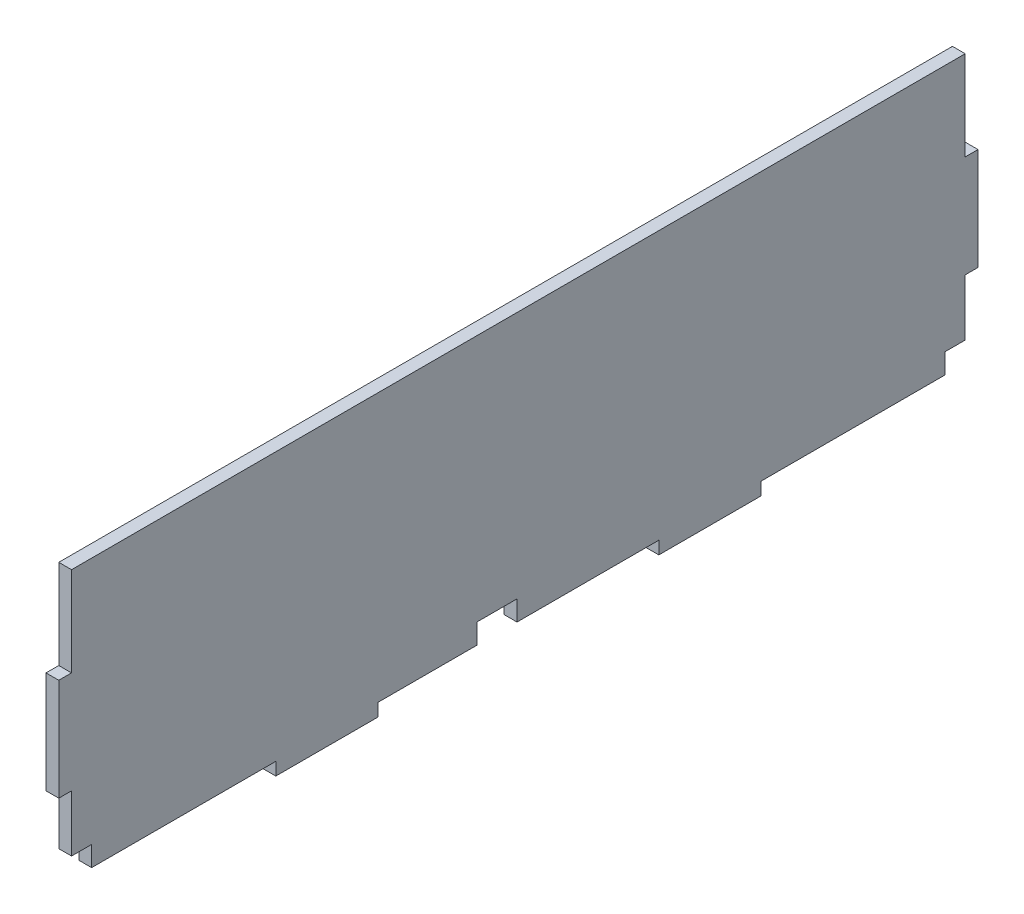
SolidWorks part; units mm, degrees
ref_plane "Front Plane" through (0, 0, 0) normal (0, 0, 1) x (1, 0, 0)
ref_plane "Top Plane" through (0, 0, 0) normal (0, 1, 0) x (1, 0, 0)
ref_plane "Right Plane" through (0, 0, 0) normal (1, 0, 0) x (0, 0, -1)
sketch "Sketch1" plane through (0, 0, 0) normal (1, 0, 0) x (0, 0, -1)
  line L0 (-105.7841, 33.834) -> (-105.7841, 8.434)
  line L1 (-105.7841, 33.834) -> (116.4659, 33.834)
  line L2 (-105.7841, 8.434) -> (-108.9591, 8.434)
  line L3 (-105.7841, -36.016) -> (-54.9841, -36.016)
  line L4 (-108.9591, 8.434) -> (-108.9591, -16.966)
  line L5 (-108.9591, -16.966) -> (-105.7841, -16.966)
  line L6 (-105.7841, -16.966) -> (-105.7841, -36.016)
  line L7 (116.4659, 33.834) -> (116.4659, 8.434)
  line L8 (116.4659, 8.434) -> (119.6409, 8.434)
  line L9 (119.6409, 8.434) -> (119.6409, -16.966)
  line L10 (119.6409, -16.966) -> (116.4659, -16.966)
  line L11 (116.4659, -16.966) -> (116.4659, -36.016)
  line L12 (-54.9841, -36.016) -> (-54.9841, -39.191)
  line L13 (-54.9841, -39.191) -> (-29.5841, -39.191)
  line L14 (-29.5841, -39.191) -> (-29.5841, -36.016)
  line L15 (-29.5841, -36.016) -> (40.2659, -36.016)
  line L16 (40.2659, -36.016) -> (40.2659, -39.191)
  line L17 (40.2659, -39.191) -> (65.6659, -39.191)
  line L18 (65.6659, -39.191) -> (65.6659, -36.016)
  line L19 (65.6659, -36.016) -> (116.4659, -36.016)
  dimension "D1" = 222.25
  dimension "D2" = 25.4
  dimension "D3" = 25.4
  dimension "D4" = 3.175
  dimension "D5" = 3.175
  dimension "D6" = 3.175
  dimension "D7" = 19.05
  dimension "D8" = 25.4
  dimension "D9" = 25.4
  dimension "D10" = 50.8
  dimension "D11" = 50.8
  dimension "D12" = 3.175
  dimension "D13" = 69.85
  dimension "D14" = 3.175
  dimension "D15" = 3.175
  dimension "D16" = 3.175
  dimension "D17" = 25.4
  dimension "D18" = 25.4
extrude "Boss-Extrude1" add sketch "Sketch1" along normal blind 3.175
sketch "Sketch2" plane through (3.175, 0, 0) normal (1, 0, 0) x (0, 0, -1)
  line L0 (116.4659, 8.434) -> (116.4659, 33.834) construction
  line L1 (-105.7841, 33.834) -> (116.4659, 33.834)
  line L2 (-105.7841, 33.834) -> (-105.7841, 30.659)
  line L3 (-105.7841, 30.659) -> (116.4659, 30.659)
  line L4 (116.4659, 33.834) -> (116.4659, 30.659)
  dimension "D1" = 3.175
extrude "Cut-Extrude1" cut sketch "Sketch2" against normal through all
sketch "Sketch3" plane through (3.175, 0, 0) normal (1, 0, 0) x (0, 0, -1)
  line L1 (-105.7841, -36.016) -> (-100.7841, -36.016)
  line L2 (-105.7841, -36.016) -> (-105.7841, -31.016)
  line L3 (-105.7841, -31.016) -> (-100.7841, -31.016)
  line L4 (-100.7841, -36.016) -> (-100.7841, -31.016)
  line L5 (116.4659, -36.016) -> (111.4659, -36.016)
  line L6 (116.4659, -36.016) -> (116.4659, -31.016)
  line L7 (116.4659, -31.016) -> (111.4659, -31.016)
  line L8 (111.4659, -36.016) -> (111.4659, -31.016)
  line L9 (-5, -31.016) -> (5, -31.016)
  line L10 (-5, -31.016) -> (-5, -36.016)
  line L11 (-5, -36.016) -> (5, -36.016)
  line L12 (5, -31.016) -> (5, -36.016)
  dimension "D1" = 5
  dimension "D2" = 5
  dimension "D3" = 5
  dimension "D4" = 5
  dimension "D5" = 5
  dimension "D6" = 10
  dimension "D7" = 5
extrude "Cut-Extrude2" cut sketch "Sketch3" against normal blind 10
